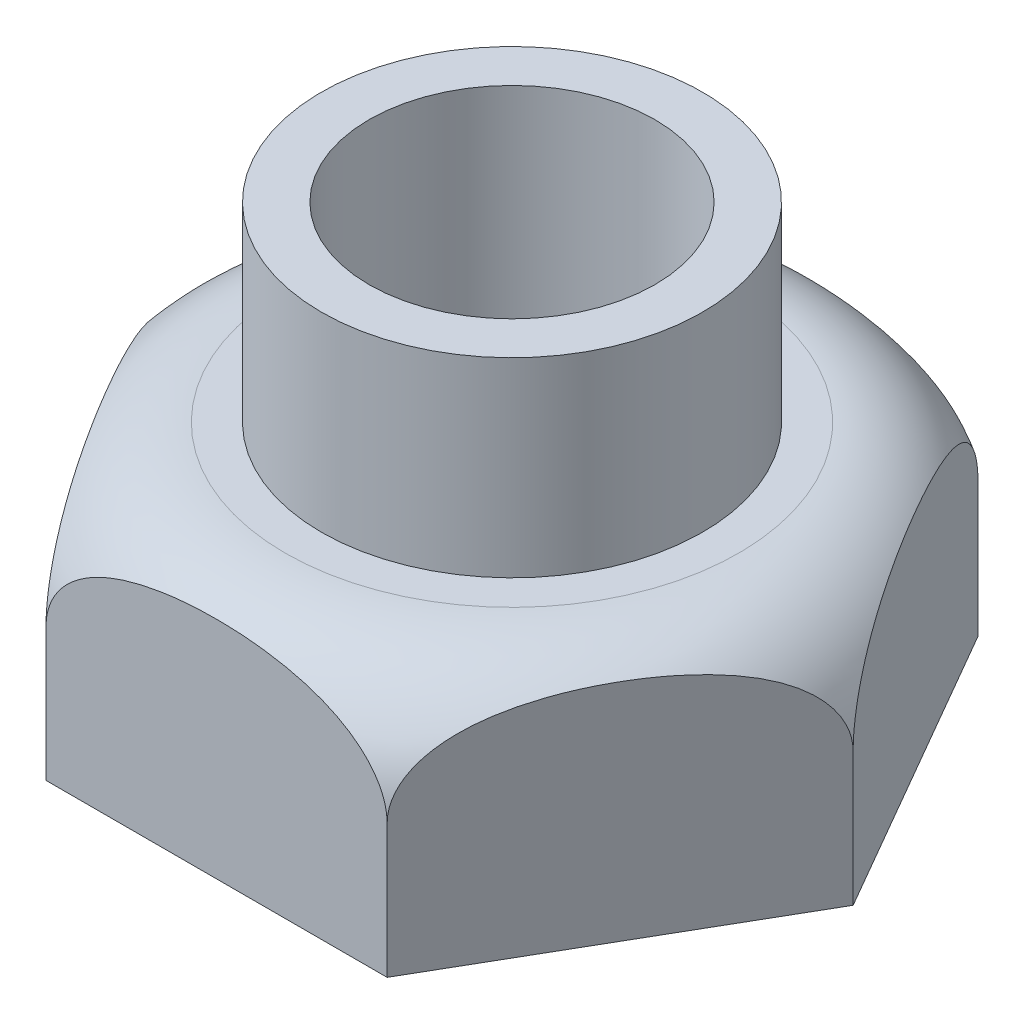
SolidWorks part; units mm, degrees
ref_plane "Front Plane" through (0, 0, 0) normal (0, 0, 1) x (1, 0, 0)
ref_plane "Top Plane" through (0, 0, 0) normal (0, 1, 0) x (1, 0, 0)
ref_plane "Right Plane" through (0, 0, 0) normal (1, 0, 0) x (0, 0, -1)
sketch "Sketch1" plane through (0, 0, 0) normal (0, 1, 0) x (1, 0, 0)
  line L1 (-89.4893, 0) -> (-44.7446, -77.5)
  line L2 (-44.7446, -77.5) -> (44.7446, -77.5)
  line L3 (44.7446, -77.5) -> (89.4893, 0)
  line L4 (89.4893, 0) -> (44.7446, 77.5)
  line L5 (44.7446, 77.5) -> (-44.7446, 77.5)
  line L6 (-44.7446, 77.5) -> (-89.4893, 0)
  circle A0 centre (0, 0) radius 77.5 construction
  dimension "D1" = 155
extrude "Boss-Extrude1" add sketch "Sketch1" along normal blind 65
sketch "Sketch4" plane through (0, 65, 0) normal (0, 1, 0) x (1, 0, 0)
  circle A0 centre (0, 0) radius 50
  circle A1 centre (0, 0) radius 37.5
  dimension "D1" = 75
  dimension "D2" = 100
extrude "Boss-Extrude2" add sketch "Sketch4" along normal blind 50
sketch "Sketch6" plane through (0, 65, 0) normal (0, 1, 0) x (1, 0, 0)
  circle A1 centre (0, 0) radius 37.5
  circle A2 centre (0, 0) radius 37.5
  dimension "D1" = 0
extrude "Cut-Extrude1" cut sketch "Sketch6" against normal blind 81
sketch "Sketch7" plane through (0, 0, 0) normal (0, 0, 1) x (1, 0, 0)
  line L0 (44.7446, 65) -> (89.4893, 65) construction
  line L1 (89.4893, 65) -> (89.4893, 0) construction
  line L2 (59.4893, 65) -> (89.4893, 65)
  line L3 (89.4893, 65) -> (89.4893, 35)
  arc A0 (59.4893, 65) -> (89.4893, 35) centre (59.4893, 35) cw
  dimension "D1" = 30
revolve "Cut-Revolve4" cut sketch "Sketch7" angle 360 about axis through (0, 115, 0) along (0, -1, 0)
